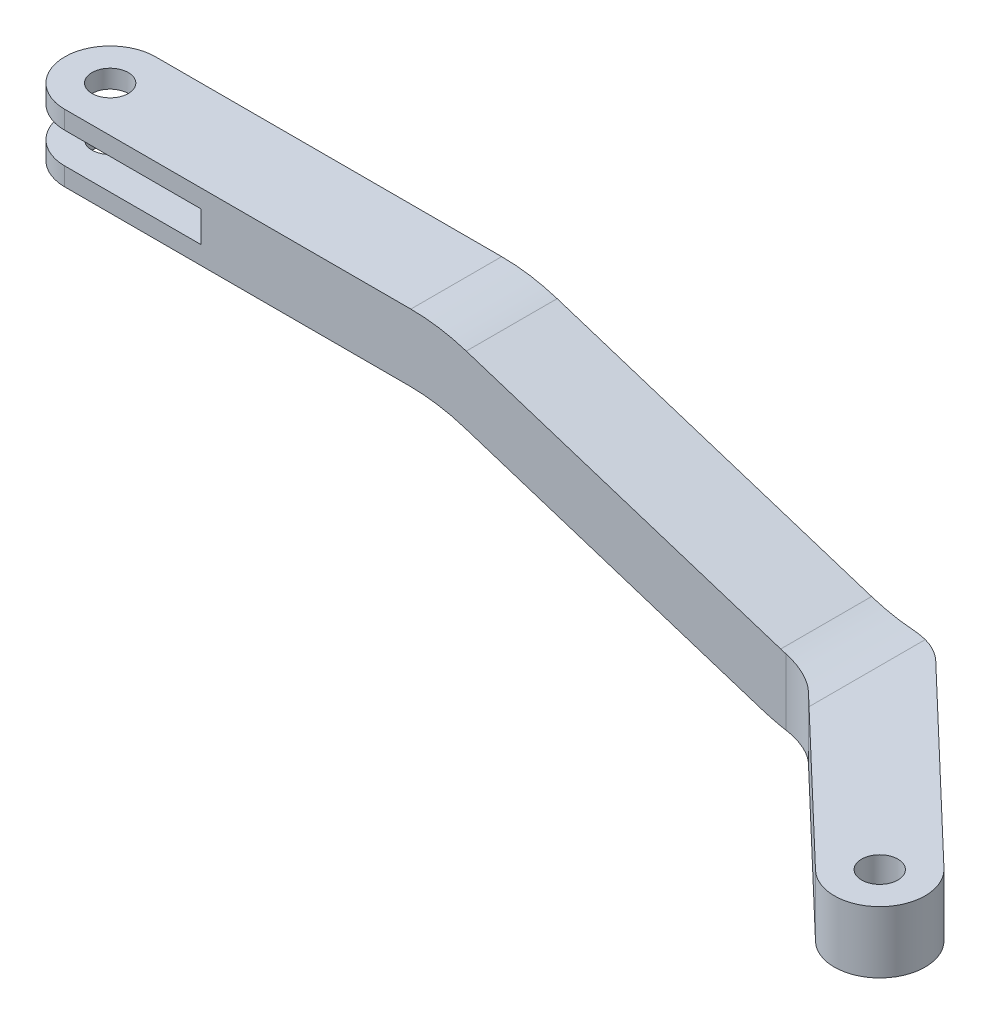
SolidWorks part; units mm, degrees
ref_plane "Front Plane" through (0, 0, 0) normal (0, 0, 1) x (1, 0, 0)
ref_plane "Top Plane" through (0, 0, 0) normal (0, 1, 0) x (1, 0, 0)
ref_plane "Right Plane" through (0, 0, 0) normal (1, 0, 0) x (0, 0, -1)
sketch "Sketch1" plane through (0, 0, 0) normal (0, 0, 1) x (1, 0, 0)
  line L0 (-14.712, 6.5) -> (8.398, 6.5)
  line L1 (8.398, 6.5) -> (28.678, 0)
  line L2 (28.678, 0) -> (-14.712, 0)
  line L3 (-14.712, 0) -> (-14.712, 6.5)
  dimension "D1" = 6.5
  dimension "D2" = 43.39
  dimension "D3" = 23.11
extrude "Boss-Extrude1" add sketch "Sketch1" along normal mid plane 5
sketch "Sketch2" plane through (0, 0, 0) normal (0, -1, 0) x (1, 0, 0)
  line L4 (-14.712, -2.5) -> (28.678, -2.5)
  line L5 (28.678, -2.5) -> (28.678, 2.5)
  line L6 (28.678, 2.5) -> (-14.712, 2.5)
  line L7 (-14.712, 2.5) -> (-14.712, -2.5)
  line L8 (-12.212, -2.5) -> (30.6824, -2.5)
  line L10 (28.678, 2.5) -> (-12.212, 2.5)
  line L12 (28.678, 2.5) -> (38.2227, 11.618)
  line L14 (-14.712, 2.5) -> (-14.712, -2.5) construction
  line L15 (41.6765, 8.0025) -> (30.6824, -2.5)
  arc A3 (-12.212, 2.5) -> (-12.212, -2.5) centre (-12.212, 0) ccw
  arc A4 (41.6765, 8.0025) -> (38.2227, 11.618) centre (39.9496, 9.8103) ccw
  dimension "D11" = 13.2
  dimension "D10" = 5
  dimension "D9" = 136.31
  dimension "D1" = 0
extrude "Boss-Extrude2" add sketch "Sketch2" along normal blind 3.4
sketch "Sketch3" plane through (0, 6.5, 0) normal (0, 1, 0) x (1, 0, 0)
  line L4 (8.398, 2.5) -> (-14.712, 2.5)
  line L5 (-14.712, 2.5) -> (-14.712, -2.5)
  line L6 (-14.712, -2.5) -> (8.398, -2.5)
  line L7 (8.398, -2.5) -> (8.398, 2.5)
  line L8 (-12.212, 2.5) -> (-14.712, 2.5)
  line L9 (-14.712, 2.5) -> (-14.712, -2.5)
  line L10 (-14.712, -2.5) -> (-12.212, -2.5)
  line L11 (8.398, -2.5) -> (8.398, 2.5)
  arc A0 (-12.212, 2.5) -> (-12.212, -2.5) centre (-12.212, 0) ccw
  line M5 (8.398, 2.5) -> (-14.712, 2.5)
  line M6 (-14.712, 2.5) -> (-14.712, -2.5)
  line M7 (-14.712, -2.5) -> (8.398, -2.5)
  dimension "D1" = 0
extrude "Cut-Extrude1" cut sketch "Sketch3" against normal through all both and the other way through all contours A0 M5 M6 | A0 L9 M7
sketch "Sketch4" plane through (0, 0, 2.5) normal (0, 0, 1) x (1, 0, 0)
  line L0 (-14.712, 2.8) -> (8.311, 2.8)
  line L1 (-14.712, 6.5) -> (-14.712, -3.4) construction
  line L2 (8.311, 2.8) -> (27.655, -3.4)
  line L3 (28.678, -3.4) -> (-12.212, -3.4) construction
  line L4 (27.655, -3.4) -> (-14.712, -3.4)
  line L5 (-14.712, -3.4) -> (-12.212, -3.4) construction
  line L6 (-14.712, -3.4) -> (-14.712, 2.8)
  line L7 (8.398, 6.5) -> (-12.212, 6.5) construction
  line L8 (28.678, 0) -> (8.398, 6.5) construction
  dimension "D1" = 3.7
  dimension "D2" = 3.55
extrude "Cut-Extrude2" cut sketch "Sketch4" against normal through all both
sketch "Sketch5" plane through (0, 0, 2.5) normal (0, 0, 1) x (1, 0, 0)
  line L0 (8.398, 6.5) -> (-12.212, 6.5) construction
  line L1 (-14.712, 5.5) -> (-4.712, 5.5)
  line L2 (-14.712, 5.5) -> (-14.712, 3.8)
  line L3 (-14.712, 3.8) -> (-4.712, 3.8)
  line L4 (-4.712, 5.5) -> (-4.712, 3.8)
  line L5 (-14.712, 6.5) -> (-14.712, 2.8) construction
  point P4 (-4.712, 4.65)
  dimension "D1" = 10
  dimension "D2" = 1.85
  dimension "D3" = 1.7
extrude "Cut-Extrude3" cut sketch "Sketch5" against normal through all both
sketch "Sketch6" plane through (0, 6.5, 0) normal (0, 1, 0) x (1, 0, 0)
  circle A0 centre (-12.212, 0) radius 1
  arc A1 (-12.212, 2.5) -> (-12.212, -2.5) centre (-12.212, 0) ccw construction
  circle A2 centre (39.9496, -9.8103) radius 1
  arc A3 (38.2227, -11.618) -> (41.6765, -8.0025) centre (39.9496, -9.8103) ccw construction
  dimension "D1" = 2
  dimension "D2" = 2
extrude "Cut-Extrude4" cut sketch "Sketch6" against normal through all both
fillet "Fillet1" radius 10 4 edges at (28.678, 0, 0) (8.398, 6.5, 0) (27.655, -3.4, 0) (8.311, 2.8, 0)
fillet "Fillet2" radius 3 2 edges at (30.6824, -1.7, -2.5) (28.678, -1.6312, 2.5)
